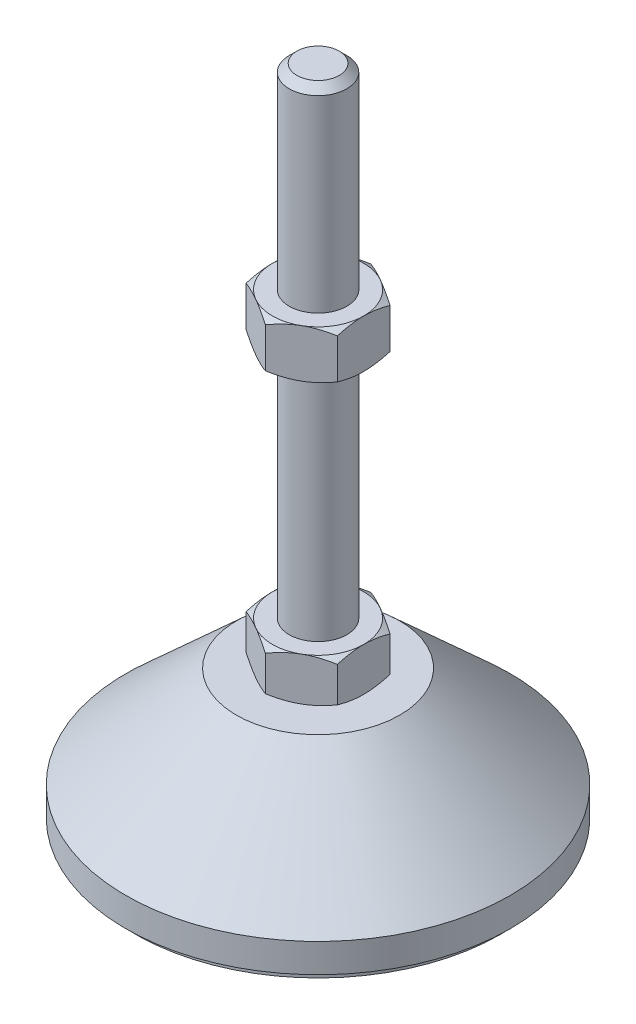
SolidWorks part; units mm, degrees
ref_plane "Спереди" through (0, 0, 0) normal (0, 0, 1) x (1, 0, 0)
ref_plane "Сверху" through (0, 0, 0) normal (0, 1, 0) x (1, 0, 0)
ref_plane "Справа" through (0, 0, 0) normal (1, 0, 0) x (0, 0, -1)
sketch "Эскиз1" plane through (0, 0, 0) normal (0, 0, 1) x (1, 0, 0)
  line L0 (0, 0) -> (-38, 0)
  line L1 (-38, 0) -> (-38, 2)
  line L2 (-38, 2) -> (-40, 2)
  line L3 (-40, 2) -> (-40, 8)
  line L4 (-40, 8) -> (-17, 29)
  line L5 (-17, 29) -> (-6, 29)
  line L12 (-6, 38) -> (-6, 136.4)
  line L13 (-6, 136.4) -> (-4.4, 138)
  line L14 (-4.4, 138) -> (0, 138)
  line L15 (0, 138) -> (0, 0) construction
  line L16 (-6, 29) -> (0, 29) construction
  line L17 (0, 0) -> (0, 138)
  line L18 (0, 0) -> (0, -7.9595) construction
  line L19 (-6, 38) -> (-6, 29)
  point P8 (-6, 87.2)
  point P23 (-11.5, 29)
  dimension "D1" = 12
  dimension "D2" = 29
  dimension "D3" = 9
  dimension "D4" = 80
  dimension "D5" = 6
  dimension "D6" = 1.6
  dimension "D7" = 45
  dimension "D8" = 34
  dimension "D9" = 2
  dimension "D10" = 100
  dimension "D11" = 6
revolve "Повернуть1" add sketch "Эскиз1" angle 360 about L17
sketch "Эскиз2" plane through (0, 29, 0) normal (0, 1, 0) x (1, 0, 0)
  line L1 (0, 10.9697) -> (-9.5, 5.4848)
  line L2 (-9.5, 5.4848) -> (-9.5, -5.4848)
  line L3 (-9.5, -5.4848) -> (0, -10.9697)
  line L4 (0, -10.9697) -> (9.5, -5.4848)
  line L5 (9.5, -5.4848) -> (9.5, 5.4848)
  line L6 (9.5, 5.4848) -> (0, 10.9697)
  circle A0 centre (0, 0) radius 9.5 construction
  dimension "D1" = 19
extrude "Бобышка-Вытянуть1" add sketch "Эскиз2" along normal up to vertex (9 mm away) up to point (-6, 38, 0)
ref_plane "Плоскость1" through (0, 87.2, 0) normal (0, 1, 0) x (1, 0, 0)
sketch "Эскиз3" plane through (0, 87.2, 0) normal (0, 1, 0) x (1, 0, 0)
  line L6 (9.5, 5.4848) -> (0, 10.9697)
  line L7 (0, 10.9697) -> (-9.5, 5.4848)
  line L8 (-9.5, 5.4848) -> (-9.5, -5.4848)
  line L9 (-9.5, -5.4848) -> (0, -10.9697)
  line L10 (0, -10.9697) -> (9.5, -5.4848)
  line L11 (9.5, -5.4848) -> (9.5, 5.4848)
  line L12 (9.5, 5.4848) -> (0, 10.9697)
  line L13 (0, 10.9697) -> (-9.5, 5.4848)
  line L14 (-9.5, 5.4848) -> (-9.5, -5.4848)
  line L15 (-9.5, -5.4848) -> (0, -10.9697)
  line L16 (0, -10.9697) -> (9.5, -5.4848)
  line L17 (9.5, -5.4848) -> (9.5, 5.4848)
  dimension "D1" = 0
extrude "Бобышка-Вытянуть2" add sketch "Эскиз3" along normal blind 10
sketch "Эскиз4" plane through (0, 0, 0) normal (0, 0, 1) x (1, 0, 0)
  line L0 (-9.5, 97.2) -> (-18.1603, 92.2)
  line L1 (-18.1603, 92.2) -> (-18.1603, 97.2)
  line L2 (-18.1603, 97.2) -> (-9.5, 97.2)
  line L3 (-18.1603, 92.2) -> (-9.5, 87.2)
  line L4 (50, 87.2) -> (-50, 87.2) construction
  line L5 (-9.5, 87.2) -> (-18.1603, 87.2)
  line L6 (-18.1603, 87.2) -> (-18.1603, 92.2)
  line L7 (-9.5, 97.2) -> (-9.5, 87.2) construction
  line L8 (-9.5, 38) -> (-17.2942, 38)
  line L9 (-17.2942, 38) -> (-17.2942, 33.5)
  line L10 (-17.2942, 33.5) -> (-9.5, 38)
  line L11 (-9.5, 29) -> (-17.2942, 33.5)
  line L12 (-17.2942, 33.5) -> (-17.2942, 29)
  line L13 (-17.2942, 29) -> (-9.5, 29)
  line L14 (0, 138) -> (0, 96.3793) construction
  dimension "D1" = 30
  dimension "D2" = 30
revolve "Вырез-Повернуть2" cut sketch "Эскиз4" angle 360 about L14
